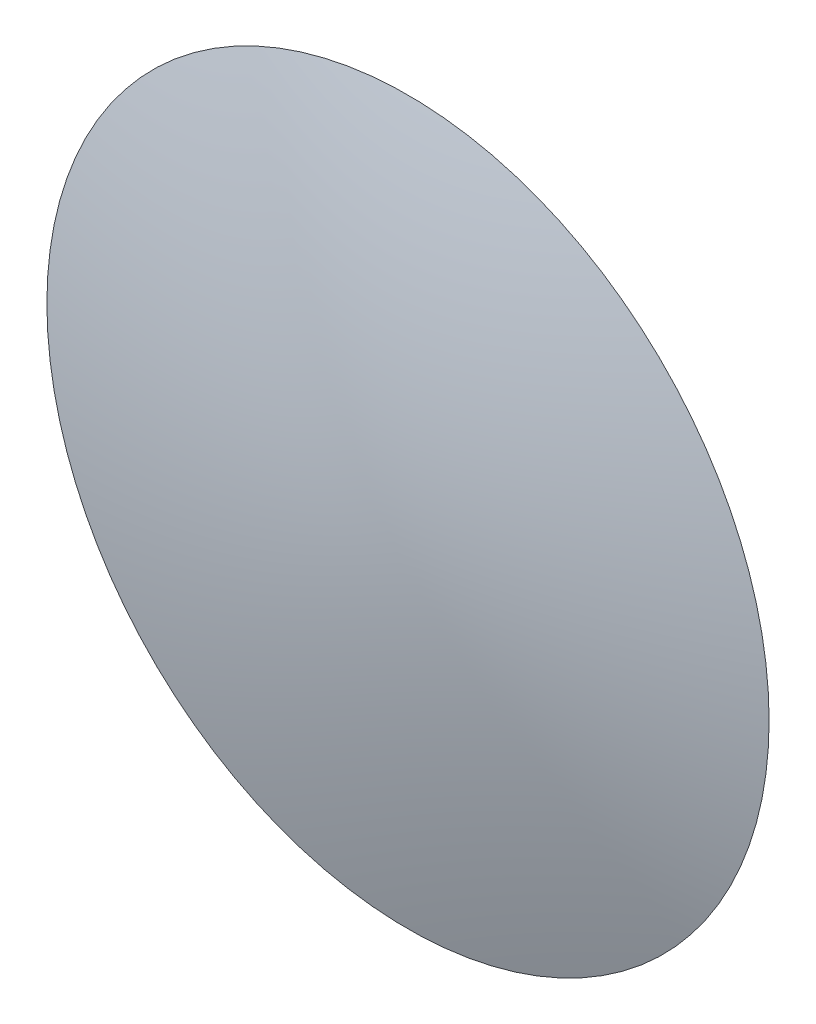
SolidWorks part; units mm, degrees
material "C-玻璃纤维"
ref_plane "前视基准面" through (0, 0, 0) normal (0, 0, 1) x (1, 0, 0)
ref_plane "上视基准面" through (0, 0, 0) normal (0, 1, 0) x (1, 0, 0)
ref_plane "右视基准面" through (0, 0, 0) normal (1, 0, 0) x (0, 0, -1)
sketch "草图2" plane through (0, 0, 0) normal (0, 0, 1) x (1, 0, 0)
  arc A0 (12.5, 0) -> (-12.5, 0) centre (0, 0) ccw
  arc A1 (12.5, 0) -> (-12.5, 0) centre (0, 0) cw
  dimension "D1" = 25
sketch "草图3" plane through (0, 0, 0) normal (0, 1, 0) x (1, 0, 0)
  line L0 (-12.5, 0) -> (12.5, 0) construction
  line L2 (0, 4.4156) -> (0, -7.3213) construction
  line L3 (0, 2.5) -> (0, -2.5)
  spline S0 degree 2 poles (0, -2.5) (-6.25, -2.5) (-15, 0) knots 0.5 0.5 0.5 1 1 1
  spline S1 degree 2 poles (-15, 0) (-6.25, 2.5) (0, 2.5) knots 0 0 0 0.5 0.5 0.5
  dimension "D1" = 2.5
  dimension "D2" = 2.5
  dimension "D3" = 15
revolve "旋转1" add sketch "草图3" angle 360 about L3
